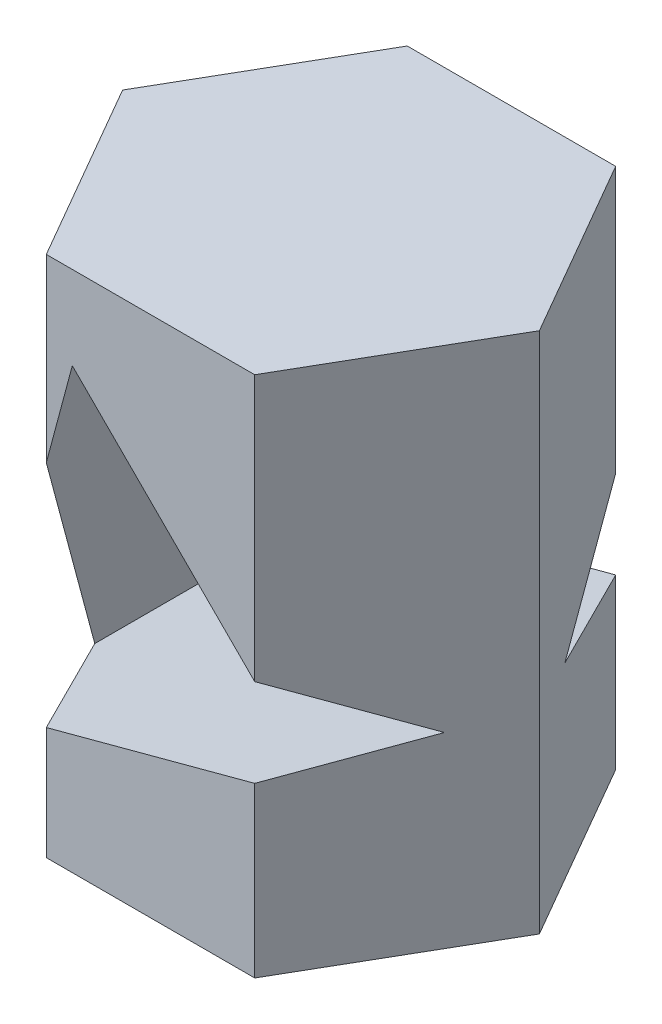
SolidWorks part; units mm, degrees
ref_plane "Front Plane" through (0, 0, 0) normal (0, 0, 1) x (1, 0, 0)
ref_plane "Top Plane" through (0, 0, 0) normal (0, 1, 0) x (1, 0, 0)
ref_plane "Right Plane" through (0, 0, 0) normal (1, 0, 0) x (0, 0, -1)
sketch "Sketch1" plane through (0, 0, 0) normal (0, 1, 0) x (1, 0, 0)
  line L1 (43.8786, 0) -> (21.9393, 38)
  line L2 (21.9393, 38) -> (-21.9393, 38)
  line L3 (-21.9393, 38) -> (-43.8786, 0)
  line L4 (-43.8786, 0) -> (-21.9393, -38)
  line L5 (-21.9393, -38) -> (21.9393, -38)
  line L6 (21.9393, -38) -> (43.8786, 0)
  circle A0 centre (0, 0) radius 38 construction
  dimension "D1" = 76
extrude "Hexagonal prism" add sketch "Sketch1" along normal blind 110 contours L3 L4 L5 L6 L1 L2
sketch "Sketch2" plane through (0, 0, 0) normal (0, 0, 1) x (1, 0, 0)
  line L0 (-16.4672, 92.4444) -> (-35.8786, 20)
  line L1 (-35.8786, 20) -> (36.5658, 39.4114)
  line L2 (36.5658, 39.4114) -> (-16.4672, 92.4444)
  line L4 (-43.8786, 110) -> (-43.8786, 0) construction
  line L5 (-21.9393, 0) -> (21.9393, 0) construction
  dimension "D1" = 75
  dimension "D2" = 8
  dimension "D3" = 20
  dimension "D4" = 15
extrude "Triangular cut" cut sketch "Sketch2" against normal through all and the other way through all
